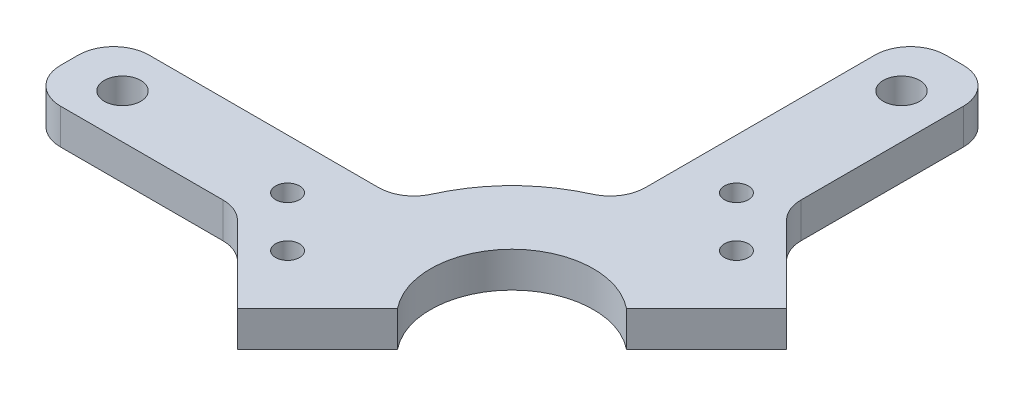
SolidWorks part; units mm, degrees
material "6061-T6 (SS)"
ref_plane "Front Plane" through (0, 0, 0) normal (0, 0, 1) x (1, 0, 0)
ref_plane "Top Plane" through (0, 0, 0) normal (0, 1, 0) x (1, 0, 0)
ref_plane "Right Plane" through (0, 0, 0) normal (1, 0, 0) x (0, 0, -1)
sketch "Sketch1" plane through (0, 0, 0) normal (0, 1, 0) x (1, 0, 0)
  circle A0 centre (0, 0) radius 14.605
  circle A1 centre (0, 0) radius 28.575
  dimension "D1" = 29.21
  dimension "D2" = 57.15
extrude "Boss-Extrude1" add sketch "Sketch1" along normal blind 6.35
sketch "Sketch2" plane through (0, 6.35, 0) normal (0, 1, 0) x (1, 0, 0)
  line L0 (73.025, -7.9375) -> (25.4, -7.9375)
  line L1 (79.375, -1.5875) -> (79.375, 1.5875)
  line L2 (25.4, -7.9375) -> (25.4, 7.9375)
  line L3 (73.025, 7.9375) -> (25.4, 7.9375)
  line L4 (79.375, -7.9375) -> (25.4, 7.9375) construction
  line L5 (25.4, -7.9375) -> (79.375, 7.9375) construction
  line L6 (0, -3.4925) -> (0, 3.4925) construction
  line L7 (52.3875, 0) -> (0, 0) construction
  arc A0 (79.375, -1.5875) -> (73.025, -7.9375) centre (73.025, -1.5875) cw
  arc A1 (79.375, 1.5875) -> (73.025, 7.9375) centre (73.025, 1.5875) ccw
  point P1 (52.3875, 0)
  dimension "D4" = 6.35
  dimension "D1" = 53.975
  dimension "D2" = 25.4
  dimension "D3" = 15.875
extrude "Boss-Extrude2" add sketch "Sketch2" against normal blind 6.35
hole_wizard "F (0.257) Diameter Hole1" positions "Sketch3" profile "Sketch4" hole size "F" standard "ANSI Inch" end condition through all
sketch "Sketch3" plane through (0, 6.35, 0) normal (0, 1, 0) x (1, 0, 0)
  line L0 (0, 0) -> (69.85, 0) construction
  point P0 (69.85, 0)
  dimension "D1" = 69.85
sketch "Sketch4" plane through (69.85, 6.35, 0) normal (1, 0, 0) x (0, 0, 1)
  line L0 (0, 0) -> (0, 6.35)
  line L1 (0, 6.35) -> (3.2639, 6.35)
  line L2 (3.2639, 6.35) -> (3.2639, 0)
  line L5 (3.2639, 0) -> (0, 0)
  line L11 (0, -6.35) -> (0, 107.95) construction
  dimension "Thru Hole Dia." = 6.5278
  dimension "Thru Hole Depth" = 6.35
pattern_circular "CirPattern1" count 4 over 360 about axis through (0, 0, 0) along (0, 1, 0) of "Boss-Extrude2", "F (0.257) Diameter Hole1"
sketch "Sketch5" plane through (0, 6.35, 0) normal (0, 1, 0) x (1, 0, 0)
  line L0 (-38.2942, -36.0491) -> (36.0491, 38.2942)
  line L1 (-38.2942, -36.0491) -> (-36.0491, -38.2942)
  line L2 (36.0491, 38.2942) -> (38.2942, 36.0491)
  line L3 (-36.0491, -38.2942) -> (38.2942, 36.0491)
  line L4 (-38.2942, -36.0491) -> (38.2942, 36.0491) construction
  line L5 (36.0491, 38.2942) -> (-36.0491, -38.2942) construction
  line L6 (-3.4925, 0) -> (3.4925, 0) construction
  point P1 (0, 0)
  dimension "D1" = 45
  dimension "D2" = 3.175
extrude "Cut-Extrude1" cut sketch "Sketch5" against normal through all
fillet "Fillet1" radius 6.35 2 edges at (-7.9375, 3.175, -27.4504) (-27.4504, 3.175, -7.9375)
sketch "Sketch7" plane through (0, 6.35, 0) normal (0, 1, 0) x (1, 0, 0)
  line L0 (-14.5131, -12.2681) -> (-25.7385, -23.4934)
  line L1 (-14.5131, -12.2681) -> (-34.7187, 7.9375)
  line L2 (-25.7385, -23.4934) -> (-45.944, -3.2878)
  line L3 (-34.7187, 7.9375) -> (-45.944, -3.2878)
  line L4 (-11.3886, -9.1436) -> (-21.2969, -19.0518) construction
  line L6 (-31.8688, 7.9375) -> (-73.025, 7.9375) construction
  dimension "D1" = 28.575
  dimension "D2" = 15.875
extrude "Boss-Extrude3" add sketch "Sketch7" against normal blind 6.35
hole_wizard "#18 (0.1695) Diameter Hole1" positions "Sketch8" profile "Sketch9" hole size "#18" standard "ANSI Inch" end condition through all
sketch "Sketch8" plane through (0, 6.35, 0) normal (0, 1, 0) x (1, 0, 0)
  line L0 (-11.3886, -9.1436) -> (-25.7385, -23.4934) construction
  line L1 (-21.2483, -19.0033) -> (-39.2088, -1.0428) construction
  line L3 (-41.2944, -7.9375) -> (-25.7385, -23.4934) construction
  point P0 (-30.2286, -10.023)
  point P2 (-39.2088, -1.0428)
  dimension "D1" = 25.4
  dimension "D2" = 12.7
  dimension "D3" = 6.35
sketch "Sketch9" plane through (-30.2286, 6.35, 10.023) normal (1, 0, 0) x (0, 0, 1)
  line L0 (0, 0) -> (0, 6.35)
  line L1 (0, 6.35) -> (2.1526, 6.35)
  line L2 (2.1526, 6.35) -> (2.1526, 0)
  line L5 (2.1526, 0) -> (0, 0)
  line L11 (0, -6.35) -> (0, 107.95) construction
  dimension "Thru Hole Dia." = 4.3053
  dimension "Thru Hole Depth" = 6.35
ref_plane "Plane2" through (0, 0, 0) normal (0.7071, 0, -0.7071) x (-0.7071, 0, -0.7071)
mirror "Mirror1" about plane through (0, 0, 0) normal (0.7071, 0, -0.7071) of "#18 (0.1695) Diameter Hole1", "Boss-Extrude3"
fillet "Fillet2" radius 6.35 2 edges at (7.9375, 3.175, -41.2944) (-41.2944, 3.175, 7.9375)
